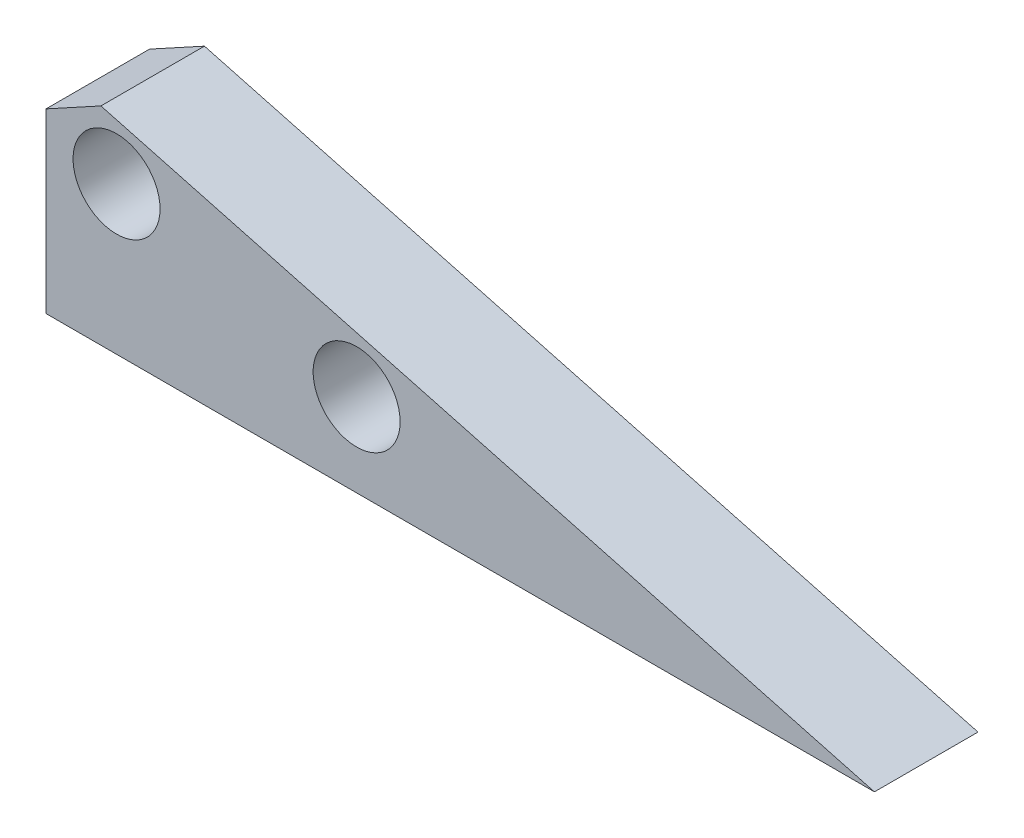
SolidWorks part; units mm, degrees
ref_plane "前视基准面" through (0, 0, 0) normal (0, 0, 1) x (1, 0, 0)
ref_plane "上视基准面" through (0, 0, 0) normal (0, 1, 0) x (1, 0, 0)
ref_plane "右视基准面" through (0, 0, 0) normal (1, 0, 0) x (0, 0, -1)
other "Configuration Table"
sketch "草图8" plane through (0, 0, 0) normal (0, 0, 1) x (1, 0, 0)
  line L3 (0, 0) -> (0, 10.718)
  line L4 (0, 10.718) -> (40, 0)
  line L5 (40, 0) -> (0, 0)
  line L6 (29.996, 0) -> (0, 8.0374)
  line L7 (2.6511, 10.0076) -> (0, 8.5583)
  circle A0 centre (3.4069, 7.1245) radius 2.1
  circle A1 centre (14.998, 4.0187) radius 2.1
  dimension "D3" = 12
  dimension "D1" = 40
  dimension "D2" = 10.718
  dimension "D4" = 7.1245
extrude "凸台-拉伸6" add sketch "草图8" along normal blind 5 contours A1 L6 A0 L3 L5 | A1 L6 L5 L4 L3 A0
